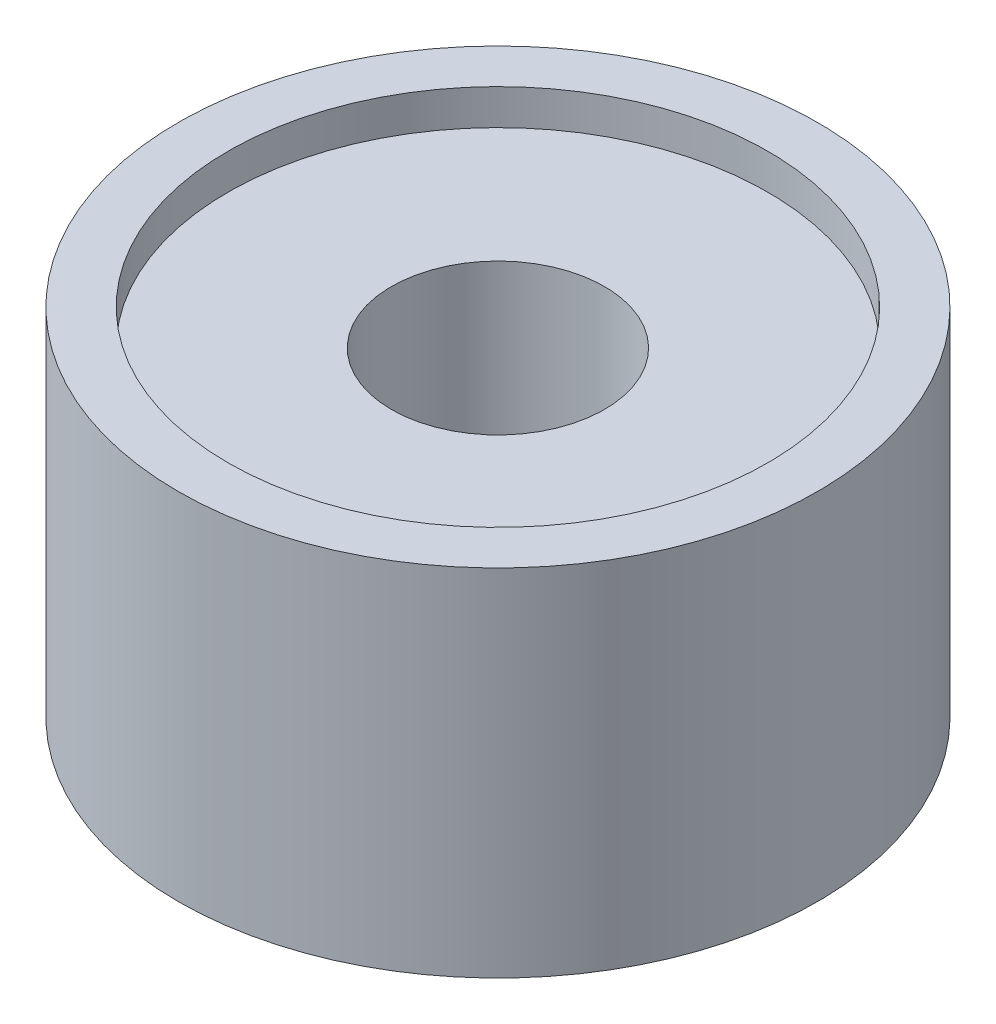
SolidWorks part; units mm, degrees
ref_plane "Front Plane" through (0, 0, 0) normal (0, 0, 1) x (1, 0, 0)
ref_plane "Top Plane" through (0, 0, 0) normal (0, 1, 0) x (1, 0, 0)
ref_plane "Right Plane" through (0, 0, 0) normal (1, 0, 0) x (0, 0, -1)
sketch "Sketch1" plane through (0, 0, 0) normal (0, 1, 0) x (1, 0, 0)
  circle A0 centre (0, 0) radius 4.5
extrude "Boss-Extrude1" add sketch "Sketch1" along normal blind 5
sketch "Sketch2" plane through (0, 5, 0) normal (0, 1, 0) x (1, 0, 0)
  circle A0 centre (0, 0) radius 1.5
extrude "Cut-Extrude1" cut sketch "Sketch2" against normal through all
sketch "Sketch3" plane through (0, 5, 0) normal (0, 1, 0) x (1, 0, 0)
  circle A0 centre (0, 0) radius 3.8
  circle A1 centre (0, 0) radius 4.5 construction
  dimension "D1" = 0.7
extrude "Cut-Extrude2" cut sketch "Sketch3" against normal blind 0.5
